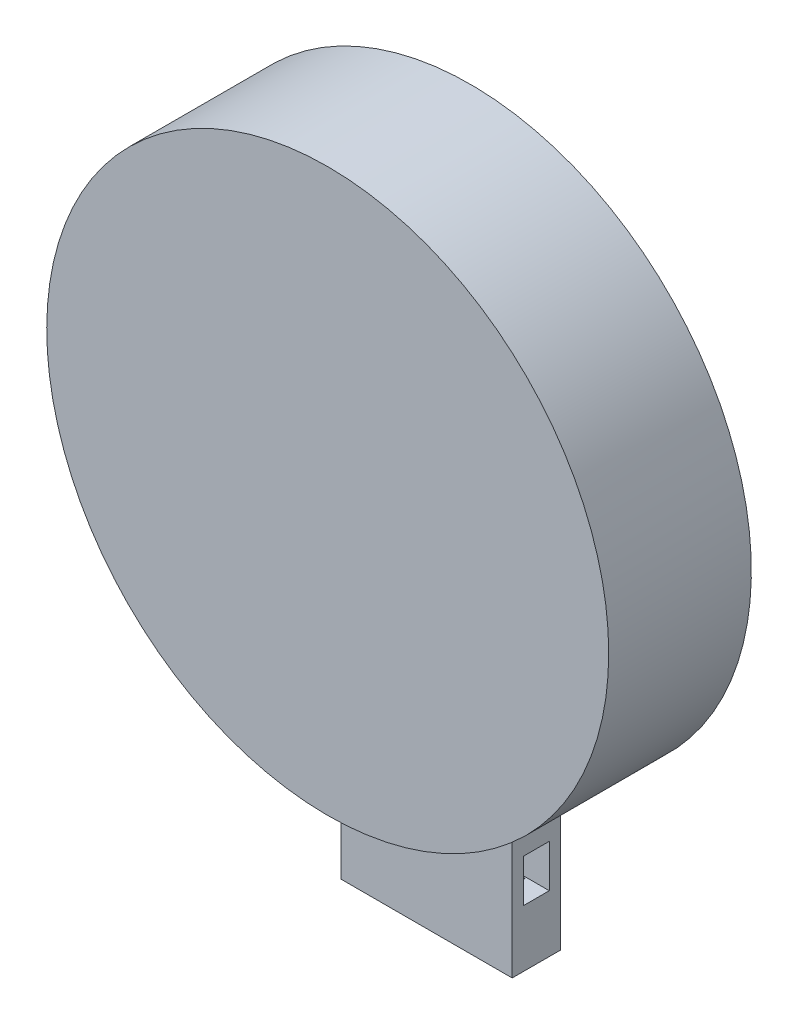
SolidWorks part; units mm, degrees
other "Markup1"
sketch "Sketch5" plane through (98.5054, -148.5054, 50) normal (0.2209, -0.9753, 0.0083) x (-0.9733, -0.2199, 0.0664)
ref_plane "Front Plane" through (0, 0, 0) normal (0, 0, 1) x (1, 0, 0)
ref_plane "Top Plane" through (0, 0, 0) normal (0, 1, 0) x (1, 0, 0)
ref_plane "Right Plane" through (0, 0, 0) normal (1, 0, 0) x (0, 0, -1)
sketch "Sketch1" plane through (0, 0, 0) normal (0, 0, 1) x (1, 0, 0)
  circle A0 centre (0, 0) radius 98.5054
extrude "Boss-Extrude1" add sketch "Sketch1" along normal blind 50
ref_plane "Plane1" through (0, -98.5054, 0) normal (0, -1, 0) x (-1, 0, 0)
sketch "Sketch2" plane through (0, -98.5054, 0) normal (0, -1, 0) x (-1, 0, 0)
  line L0 (98.5054, 0) -> (-98.5054, 0) construction
  line L1 (-31.666, -17) -> (28.334, -17)
  line L2 (-31.666, -17) -> (-31.666, 0)
  line L3 (-31.666, 0) -> (28.334, 0)
  line L4 (28.334, -17) -> (28.334, 0)
  line L5 (-31.666, -17) -> (28.334, 0) construction
  line L6 (-31.666, 0) -> (28.334, -17) construction
  point P0 (-1.666, -8.5)
  dimension "D1" = 60
  dimension "D2" = 17
extrude "Boss-Extrude2" add sketch "Sketch2" along normal blind 50 and the other way up to surface
sketch "Sketch3" plane through (0, -148.5054, 0) normal (0, -1, 0) x (1, 0, 0)
  line L0 (-28.334, 0) -> (31.666, 0) construction
  line L1 (23.666, 4.5) -> (-20.334, 4.5)
  line L2 (23.666, 4.5) -> (23.666, 12.5)
  line L3 (23.666, 12.5) -> (-20.334, 12.5)
  line L4 (-20.334, 4.5) -> (-20.334, 12.5)
  line L5 (23.666, 4.5) -> (-20.334, 12.5) construction
  line L6 (23.666, 12.5) -> (-20.334, 4.5) construction
  line L8 (31.666, 0) -> (31.666, 17) construction
  line L10 (-28.334, 17) -> (-28.334, 0) construction
  point P0 (1.666, 8.5)
  dimension "D1" = 4.5
  dimension "D2" = 8
  dimension "D3" = 8
  dimension "D4" = 8
extrude "Cut-Extrude1" cut sketch "Sketch3" against normal blind 40
sketch "Sketch4" plane through (-28.334, 0, 0) normal (-1, 0, 0) x (0, 0, 1)
  line L0 (0, -148.5054) -> (0, -94.3425) construction
  line L1 (4, -113.5054) -> (13, -113.5054)
  line L2 (4, -113.5054) -> (4, -128.5054)
  line L3 (4, -128.5054) -> (13, -128.5054)
  line L4 (13, -113.5054) -> (13, -128.5054)
  line L5 (8.5, -128.5054) -> (8.5, -113.5054) construction
  line L6 (4, -121.0054) -> (13, -121.0054) construction
  line L7 (17, -148.5054) -> (17, -94.3425) construction
  line L8 (17, -148.5054) -> (0, -148.5054) construction
  point P196 (8.5, -121.0054)
  dimension "D1" = 4
  dimension "D2" = 4
  dimension "D3" = 15
  dimension "D4" = 20
extrude "Cut-Extrude2" cut sketch "Sketch4" against normal through all
